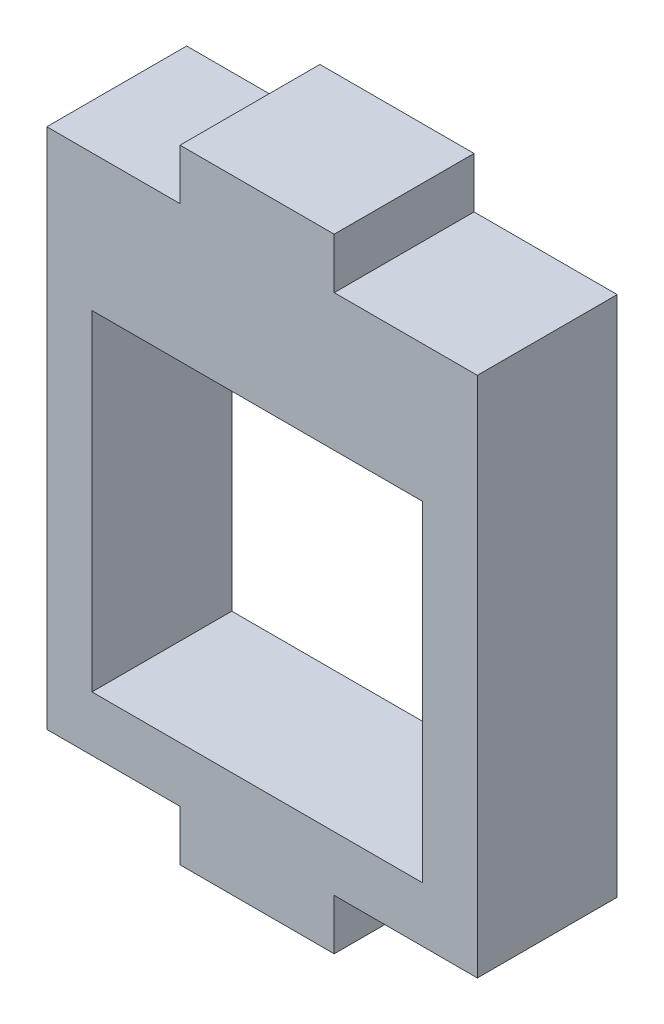
SolidWorks part; units mm, degrees
ref_plane "Front Plane" through (0, 0, 0) normal (0, 0, 1) x (1, 0, 0)
ref_plane "Top Plane" through (0, 0, 0) normal (0, 1, 0) x (1, 0, 0)
ref_plane "Right Plane" through (0, 0, 0) normal (1, 0, 0) x (0, 0, -1)
sketch "Sketch1" plane through (0, 0, 0) normal (0, 0, 1) x (1, 0, 0)
  line L0 (-15.2353, 17.8836) -> (-15.2353, 2.8836)
  line L1 (-15.2353, 2.8836) -> (-0.2353, 2.8836)
  line L2 (-0.2353, 2.8836) -> (-0.2353, 17.8836)
  line L3 (-0.2353, 17.8836) -> (2.2647, 17.8836)
  line L4 (2.2647, 17.8836) -> (2.2647, 0.3836)
  line L5 (2.2647, 0.3836) -> (-17.7353, 0.3836)
  line L6 (-17.7353, 0.3836) -> (-17.7353, 17.8836)
  line L7 (-17.7353, 17.8836) -> (-15.2353, 17.8836)
  dimension "D1" = 2.5
  dimension "D2" = 15
  dimension "D3" = 2.5
  dimension "D4" = 15
  dimension "D5" = 15
  dimension "D6" = 2.5
extrude "Boss-Extrude1" add sketch "Sketch1" along normal blind 6.35
sketch "Sketch2" plane through (0, 0, 0) normal (0, 0, 1) x (1, 0, 0)
  line L5 (-17.7353, 17.8836) -> (2.2647, 17.8836)
  line L6 (-17.7353, 17.8836) -> (-17.7353, 20.3836)
  line L7 (-17.7353, 20.3836) -> (2.2647, 20.3836)
  line L8 (2.2647, 17.8836) -> (2.2647, 20.3836)
  dimension "D1" = 20
  dimension "D2" = 2.5
extrude "Boss-Extrude2" add sketch "Sketch2" along normal through all
sketch "Sketch4" plane through (0, 0, 6.35) normal (0, 0, 1) x (1, 0, 0)
  line L0 (-17.7353, 0.3836) -> (2.2647, 0.3836) construction
  line L1 (-17.7353, 20.3836) -> (2.2647, 20.3836)
  line L2 (-17.7353, 20.3836) -> (-17.7353, 24.0836)
  line L3 (-17.7353, 24.0836) -> (-11.2353, 24.0836)
  line L4 (2.2647, 20.3836) -> (2.2647, 24.0836)
  line L6 (-11.2353, 24.0836) -> (-11.2353, 26.3836)
  line L7 (-11.2353, 26.3836) -> (-4.2353, 26.3836)
  line L8 (-4.2353, 24.0836) -> (-4.2353, 26.3836)
  line L9 (-11.2353, 0.3836) -> (-4.2353, 0.3836)
  line L10 (-11.2353, 0.3836) -> (-11.2353, -1.9164)
  line L11 (-11.2353, -1.9164) -> (-4.2353, -1.9164)
  line L12 (-4.2353, 0.3836) -> (-4.2353, -1.9164)
  line L13 (-17.7353, 20.3836) -> (-17.7353, 0.3836) construction
  line L14 (2.2647, 0.3836) -> (2.2647, 20.3836) construction
  line L15 (-4.2353, 24.0836) -> (2.2647, 24.0836)
  dimension "D1" = 3.7
  dimension "D2" = 20
  dimension "D3" = 7
  dimension "D4" = 2.3
  dimension "D5" = 6.5
  dimension "D6" = 6.5
  dimension "D7" = 7
  dimension "D8" = 2.3
  dimension "D9" = 6.5
extrude "Boss-Extrude3" add sketch "Sketch4" against normal blind 6.35
sketch "Sketch5" plane through (0, 0, 6.35) normal (0, 0, 1) x (1, 0, 0)
  line L0 (-17.7353, 0.3836) -> (-11.2353, 0.3836) construction
  line L1 (-17.7353, 24.0836) -> (-17.2853, 24.0836)
  line L2 (-17.7353, 24.0836) -> (-17.7353, 0.3836)
  line L3 (-17.7353, 0.3836) -> (-17.2853, 0.3836)
  line L4 (-17.2853, 24.0836) -> (-17.2853, 0.3836)
  dimension "D1" = 0.45
extrude "Cut-Extrude1" cut sketch "Sketch5" against normal blind 10
